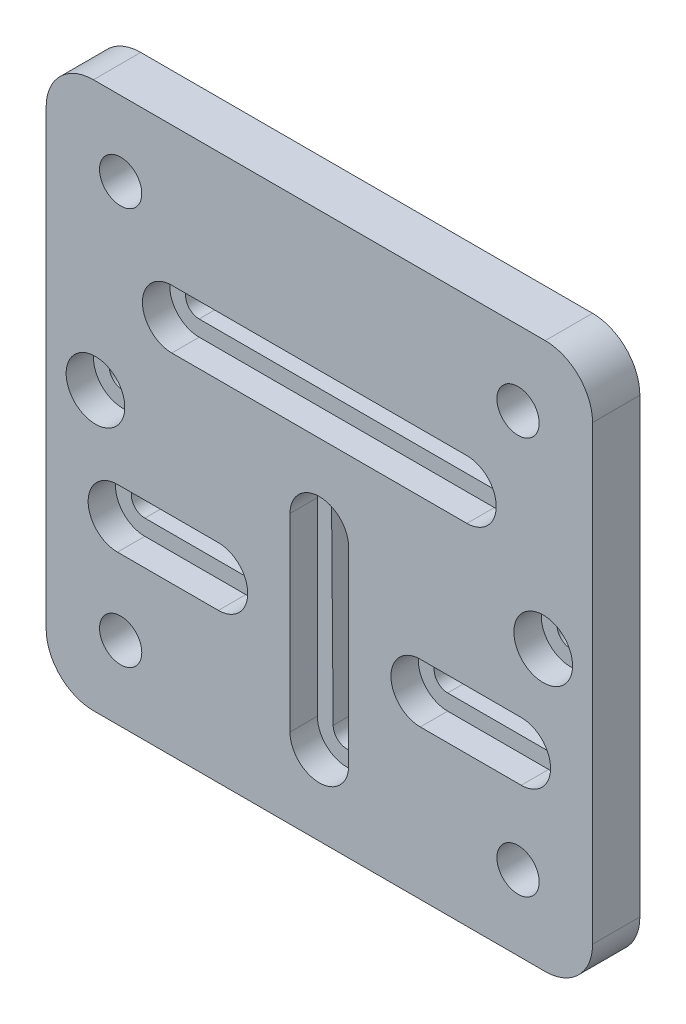
SolidWorks part; units mm, degrees
ref_plane "Front Plane" through (0, 0, 0) normal (0, 0, 1) x (1, 0, 0)
ref_plane "Top Plane" through (0, 0, 0) normal (0, 1, 0) x (1, 0, 0)
ref_plane "Right Plane" through (0, 0, 0) normal (1, 0, 0) x (0, 0, -1)
sketch "Sketch1" plane through (0, 0, 0) normal (0, 0, 1) x (1, 0, 0)
  line L0 (0, 54.9999) -> (0, 27.0599) construction
  line L1 (-54.9999, -54.9999) -> (54.9999, -54.9999)
  line L2 (-54.9999, -54.9999) -> (-54.9999, 54.9999)
  line L3 (-54.9999, 54.9999) -> (54.9999, 54.9999)
  line L4 (54.9999, -54.9999) -> (54.9999, 54.9999)
  line L5 (-54.9999, -54.9999) -> (54.9999, 54.9999) construction
  line L6 (-54.9999, 54.9999) -> (54.9999, -54.9999) construction
  line L7 (0, 27.0599) -> (0, 15.2489) construction
  line L8 (-29.7053, 21.1544) -> (29.7053, 21.1544) construction
  line L9 (0, 27.0599) -> (0, 15.2489) construction
  line L11 (-29.7053, 15.2489) -> (29.7053, 15.2489)
  line L12 (-29.7053, 15.2489) -> (-29.7053, 27.0599) construction
  line L13 (-29.7053, 27.0599) -> (29.7053, 27.0599)
  line L14 (29.7053, 15.2489) -> (29.7053, 27.0599) construction
  line L15 (-29.7053, 15.2489) -> (29.7053, 27.0599) construction
  line L16 (-29.7053, 27.0599) -> (29.7053, 15.2489) construction
  arc A0 (-29.7053, 27.0599) -> (-29.7053, 15.2489) centre (-29.7053, 21.1544) ccw
  arc A1 (29.7053, 27.0599) -> (29.7053, 15.2489) centre (29.7053, 21.1544) cw
  point P0 (0, 0)
  point P11 (0, 21.1544)
  point P12 (0, 21.1544)
  point P13 (0, 21.1544)
  point P19 (-35.6108, 21.1544)
  point P21 (35.6108, 21.1544)
  dimension "D1" = 109.9998
  dimension "D2" = 109.9998
  dimension "D3" = 27.94
  dimension "D4" = 11.811
  dimension "D5" = 71.2216
extrude "Boss-Extrude1" add sketch "Sketch1" against normal blind 9.525 contours L2 L1 L4 L3
sketch "Sketch2" plane through (0, 0, 0) normal (0, 0, 1) x (1, 0, 0)
  line L0 (-5.9055, -0.8255) -> (5.9055, -0.8255) construction
  line L1 (-29.7053, 27.0599) -> (29.7053, 27.0599) construction
  line L2 (-29.7053, 15.2489) -> (29.7053, 15.2489) construction
  line L3 (-29.7053, 27.0599) -> (29.7053, 27.0599)
  line L4 (-29.7053, 15.2489) -> (29.7053, 15.2489)
  line L5 (-5.9055, -0.8255) -> (-5.9055, -38.9255)
  line L6 (5.9055, -0.8255) -> (5.9055, -38.9255)
  line L7 (-5.9055, -38.9255) -> (5.9055, -38.9255) construction
  line L8 (20.32, -19.0284) -> (40.64, -19.0284) construction
  line L9 (58.5953, -19.0284) -> (80.4443, -19.0284) construction
  line L10 (45.0685, -4.8425) -> (45.0685, 6.9685) construction
  line L11 (45.0685, -37.4409) -> (45.0685, -59.29) construction
  line L12 (20.32, -24.9339) -> (20.32, -13.1229) construction
  line L13 (40.64, -24.9339) -> (40.64, -13.1229) construction
  line L14 (20.32, -13.1229) -> (40.64, -13.1229)
  line L15 (100.0685, 1.063) -> (-9.9315, 1.063) construction
  line L16 (20.32, -24.9339) -> (40.64, -24.9339)
  line L17 (0, 15.2489) -> (0, -54.9999) construction
  line L18 (0, -5.2388) -> (0, 5.2388) construction
  line L19 (-20.32, -13.1229) -> (-40.64, -13.1229)
  line L20 (-20.32, -24.9339) -> (-40.64, -24.9339)
  line L21 (-54.9999, -54.9999) -> (54.9999, -54.9999) construction
  line L22 (0, -38.9255) -> (0, -0.8255) construction
  line L23 (-29.7053, 21.1544) -> (29.7053, 21.1544) construction
  arc A0 (29.7053, 15.2489) -> (29.7053, 27.0599) centre (29.7053, 21.1544) ccw construction
  arc A1 (-29.7053, 27.0599) -> (-29.7053, 15.2489) centre (-29.7053, 21.1544) ccw construction
  arc A2 (29.7053, 15.2489) -> (29.7053, 27.0599) centre (29.7053, 21.1544) ccw
  arc A3 (-29.7053, 27.0599) -> (-29.7053, 15.2489) centre (-29.7053, 21.1544) ccw
  arc A4 (-5.9055, -0.8255) -> (5.9055, -0.8255) centre (0, -0.8255) cw
  arc A5 (-5.9055, -38.9255) -> (5.9055, -38.9255) centre (0, -38.9255) ccw
  arc A6 (20.32, -13.1229) -> (20.32, -24.9339) centre (20.32, -19.0284) ccw
  arc A7 (40.64, -13.1229) -> (40.64, -24.9339) centre (40.64, -19.0284) cw
  arc A8 (-20.32, -13.1229) -> (-20.32, -24.9339) centre (-20.32, -19.0284) cw
  arc A9 (-40.64, -13.1229) -> (-40.64, -24.9339) centre (-40.64, -19.0284) ccw
  circle A10 centre (45.0685, 1.063) radius 5.9055
  circle A11 centre (-45.0685, 1.063) radius 5.9055
  point P9 (0, 0)
  point P26 (20.32, -19.0284)
  point P28 (40.64, -19.0284)
  point P37 (45.0685, 1.063)
  point P44 (0, -19.8755)
  point P45 (0, 21.1544)
  dimension "D1" = 11.811
  dimension "D2" = 38.1
  dimension "D3" = 0
  dimension "D4" = 0
  dimension "D5" = 11.811
  dimension "D6" = 20.32
  dimension "D7" = 20.32
  dimension "D8" = 0
  dimension "D9" = 11.811
extrude "Cut-Extrude1" cut sketch "Sketch2" against normal blind 5.5118
sketch "Sketch3" plane through (0, 0, 0) normal (0, 0, 1) x (1, 0, 0)
  line L0 (-29.7053, 21.1544) -> (29.7053, 21.1544) construction
  line L1 (-29.7053, 21.1544) -> (29.7053, 21.1544) construction
  line L2 (-29.7053, 18.4239) -> (-29.7053, 23.8849) construction
  line L3 (0, -5.2388) -> (0, 5.2388) construction
  line L4 (-29.7053, 23.8849) -> (29.7053, 23.8849)
  line L5 (-29.7053, 18.4239) -> (29.7053, 18.4239)
  line L6 (3.048, -0.8255) -> (-3.048, -0.8255) construction
  line L7 (0, -0.8255) -> (0, -38.9255) construction
  line L8 (-2.7305, -38.9255) -> (2.7305, -38.9255) construction
  line L9 (3.048, -0.8255) -> (2.7305, -38.9255)
  line L10 (-2.7305, -38.9255) -> (-3.048, -0.8255)
  line L11 (20.32, -24.9339) -> (20.32, -13.1229) construction
  line L12 (40.64, -24.9339) -> (40.64, -13.1229) construction
  line L13 (20.32, -16.2979) -> (40.64, -16.2979)
  line L14 (20.32, -21.7589) -> (40.64, -21.7589)
  line L15 (-20.32, -16.2979) -> (-40.64, -16.2979)
  line L16 (-20.32, -21.7589) -> (-40.64, -21.7589)
  arc A0 (-29.7053, 23.8849) -> (-29.7053, 18.4239) centre (-29.7053, 21.1544) ccw
  arc A1 (29.7053, 23.8849) -> (29.7053, 18.4239) centre (29.7053, 21.1544) cw
  arc A2 (-2.7305, -38.9255) -> (2.7305, -38.9255) centre (0, -38.9255) ccw
  arc A3 (3.048, -0.8255) -> (-3.048, -0.8255) centre (0, -0.8255) ccw
  arc A4 (20.32, -16.2979) -> (20.32, -21.7589) centre (20.32, -19.0284) ccw
  arc A5 (40.64, -16.2979) -> (40.64, -21.7589) centre (40.64, -19.0284) cw
  circle A6 centre (45.0685, 1.063) radius 2.7305
  circle A7 centre (-45.0685, 1.063) radius 2.7305
  arc A8 (-20.32, -16.2979) -> (-20.32, -21.7589) centre (-20.32, -19.0284) cw
  arc A9 (-40.64, -16.2979) -> (-40.64, -21.7589) centre (-40.64, -19.0284) ccw
  circle A10 centre (0, -19.8755) radius 1.6218 construction
  circle A11 centre (0, 21.1544) radius 2.0648 construction
  point P4 (-29.7053, 21.1544)
  point P14 (0, 0)
  point P18 (0, -38.9255)
  point P20 (45.0685, 1.063)
  point P23 (40.64, -19.0284)
  point P25 (20.32, -19.0284)
  dimension "D5" = 2.7305
  dimension "D6" = 2.7305
  dimension "D7" = 5.461
  dimension "D1" = 5.461
  dimension "D2" = 6.096
  dimension "D3" = 38.1
  dimension "D4" = 5.461
  dimension "D8" = 0
extrude "Cut-Extrude3" cut sketch "Sketch3" against normal through all contours A1 L4 A0 L5 | L9 A3 L10 A2 | L15 A9 L16 A8 | A5 L13 A4 L14 | A7 | A6
sketch "Sketch4" plane through (0, 0, 0) normal (0, 0, 1) x (1, 0, 0)
  line L2 (5.2248, 0) -> (-5.2248, 0) construction
  line L3 (0, -5.2248) -> (0, 5.2248) construction
  circle A0 centre (-39.9987, -39.9987) radius 4.2545
  circle A1 centre (-39.9987, 39.9987) radius 4.2545
  circle A2 centre (39.9987, -39.9987) radius 4.2545
  circle A3 centre (39.9987, 39.9987) radius 4.2545
  point P0 (-39.9987, -39.9987)
  dimension "D3" = 8.509
  dimension "D1" = 39.9987
  dimension "D2" = 39.9987
extrude "Cut-Extrude4" cut sketch "Sketch4" against normal through all
ref_plane "Front_Alum_Axis" through (0, 21.1544, 0) normal (0, 1, 0) x (1, 0, 0)
fillet "Fillet1" radius 9.525 4 edges at (-54.9999, 54.9999, -4.7625) (-54.9999, -54.9999, -4.7625) (54.9999, -54.9999, -4.7625) (54.9999, 54.9999, -4.7625)
